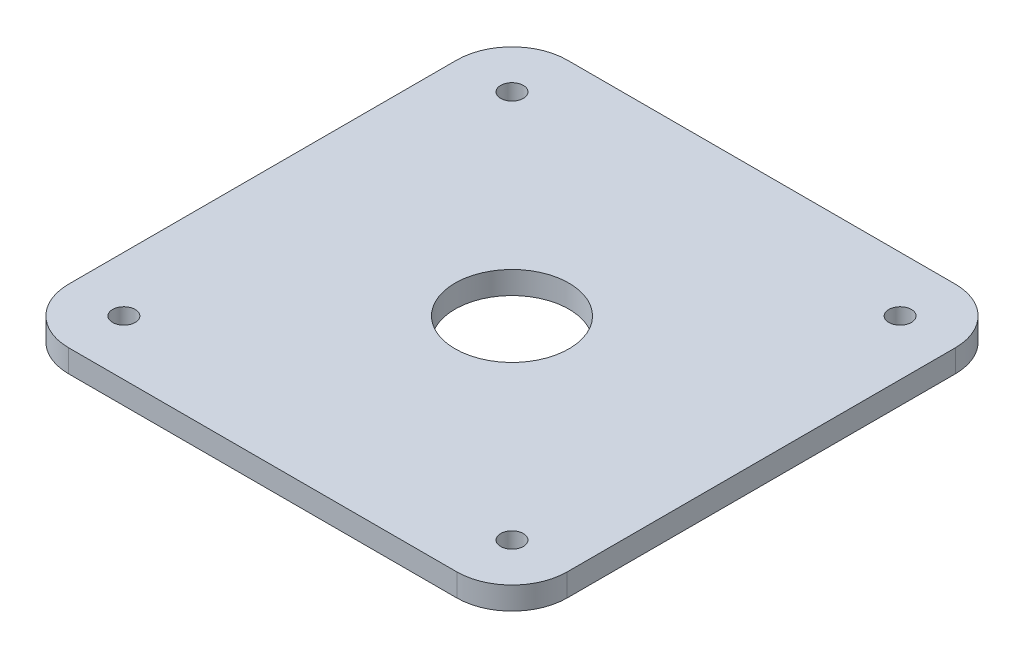
SolidWorks part; units mm, degrees
material "Pino"
ref_plane "Alzado" through (0, 0, 0) normal (0, 0, 1) x (1, 0, 0)
ref_plane "Planta" through (0, 0, 0) normal (0, 1, 0) x (1, 0, 0)
ref_plane "Vista lateral" through (0, 0, 0) normal (1, 0, 0) x (0, 0, -1)
sketch "Croquis1" plane through (0, 0, 0) normal (0, 1, 0) x (1, 0, 0)
  line L1 (-109, 140) -> (109, 140)
  line L2 (-140, 109) -> (-140, -109)
  line L3 (-109, -140) -> (109, -140)
  line L4 (140, 109) -> (140, -109)
  line L5 (-140, 140) -> (140, -140) construction
  line L6 (-140, -140) -> (140, 140) construction
  arc A0 (109, -140) -> (140, -109) centre (109, -109) ccw
  arc A1 (-140, -109) -> (-109, -140) centre (-109, -109) ccw
  arc A2 (109, 140) -> (140, 109) centre (109, 109) cw
  arc A3 (-109, 140) -> (-140, 109) centre (-109, 109) ccw
  circle A4 centre (0, 0) radius 32
  circle A5 centre (-109, 109) radius 6.35
  circle A6 centre (109, 109) radius 6.35
  circle A7 centre (109, -109) radius 6.35
  circle A8 centre (-109, -109) radius 6.35
  point P0 (0, 0)
  dimension "D3" = 31
  dimension "D4" = 12.7
  dimension "D5" = 64
  dimension "D1" = 280
  dimension "D2" = 280
extrude "Saliente-Extruir1" add sketch "Croquis1" along normal blind 12.7
